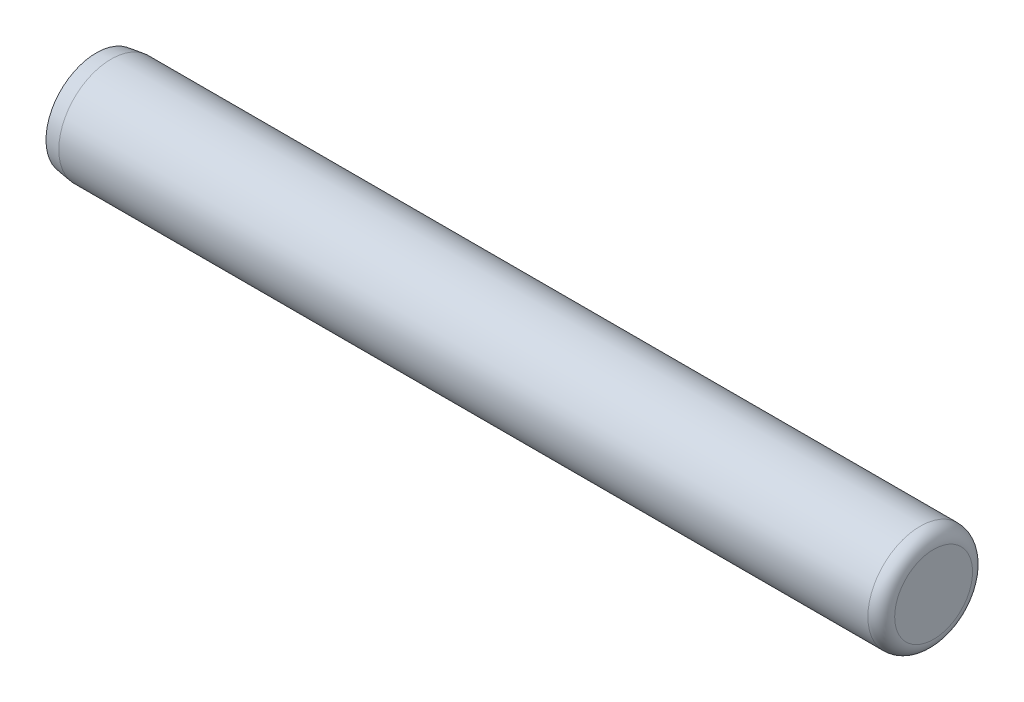
SolidWorks part; units mm, degrees
ref_plane "Front" through (0, 0, 0) normal (0, 0, 1) x (1, 0, 0)
ref_plane "Top" through (0, 0, 0) normal (0, 1, 0) x (1, 0, 0)
ref_plane "Right" through (0, 0, 0) normal (1, 0, 0) x (0, 0, -1)
sketch "Sketch1" plane through (0, 0, 0) normal (1, 0, 0) x (0, 0, -1)
  circle A0 centre (0, 0) radius 1.5875 construction
  dimension "Diameter" = 3.175
sketch "Sketch2" plane through (0, 0, 0) normal (0, 0, 1) x (1, 0, 0)
  line L0 (-12.7, 1.524) -> (-12.2482, 1.5875) construction
  line L1 (-12.7, 1.5875) -> (12.7, 1.5875) construction
  line L2 (-12.7, 1.5875) -> (-12.7, -1.5875) construction
  line L3 (-12.7, -1.5875) -> (12.7, -1.5875) construction
  line L4 (12.7, 1.5875) -> (12.7, -1.5875) construction
  line L5 (0, -1.5875) -> (0, 1.5875) construction
  line L6 (-12.7, 0) -> (12.7, 0) construction
  arc A0 (12.2936, 1.5875) -> (12.7, 1.1811) centre (12.2936, 1.1811) cw construction
  point P0 (0, 0)
  dimension "D1" = 8
  dimension "Crown Radius (R)" = 0.4064
  dimension "Length" = 25.4
  dimension "Crown Height (C)" = 0.4064
  dimension "Point Diameter (B)" = 3.048
  dimension "Length - Chamfer and Fillet (Le)" = 24.5418
sketch "Sketch3" plane through (0, 0, 0) normal (0, 0, 1) x (1, 0, 0)
  line L0 (-12.7, 0) -> (12.7, 0)
  line L1 (12.7, 0) -> (12.7, 1.1811)
  line L2 (-12.7, 0) -> (-12.7, 1.524)
  line L3 (-12.7, 1.524) -> (-12.2482, 1.5875)
  line L4 (-12.2482, 1.5875) -> (12.2936, 1.5875)
  arc A0 (12.7, 1.1811) -> (12.2936, 1.5875) centre (12.2936, 1.1811) ccw construction
  arc A1 (12.7, 1.1811) -> (12.2936, 1.5875) centre (12.2936, 1.1811) ccw
revolve "Revolve1" add sketch "Sketch3" angle 360 about L0
